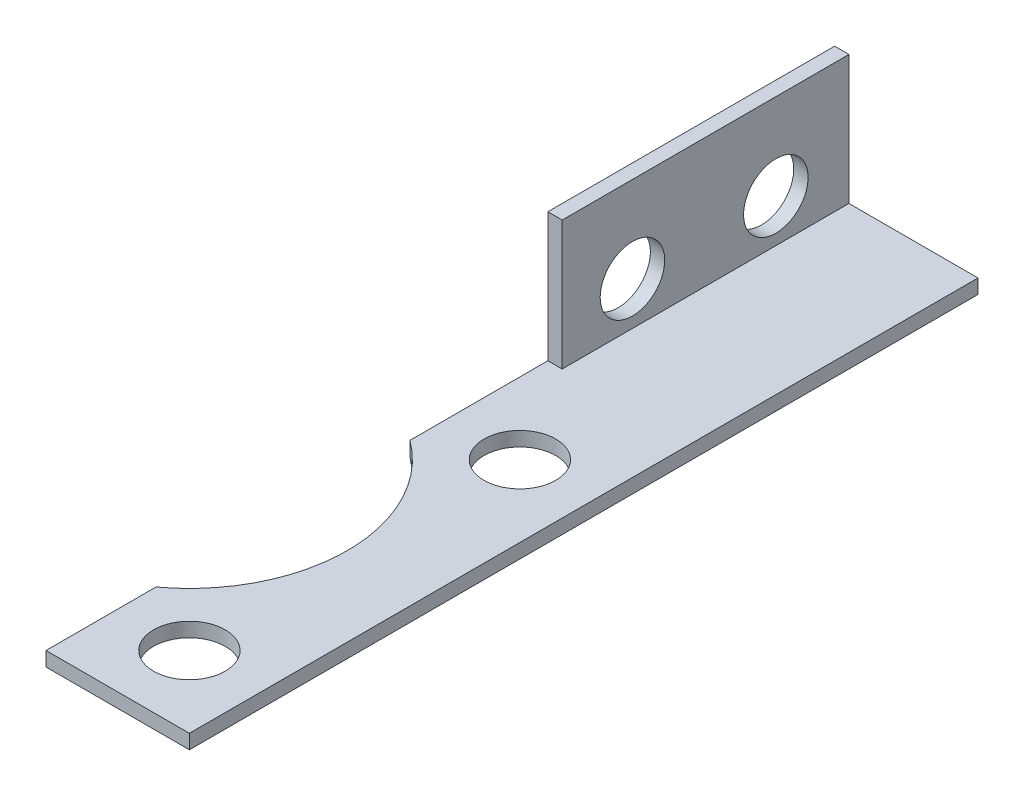
SolidWorks part; units mm, degrees
material "7075-T6 (SN)"
ref_plane "Front Plane" through (0, 0, 0) normal (0, 0, 1) x (1, 0, 0)
ref_plane "Top Plane" through (0, 0, 0) normal (0, 1, 0) x (1, 0, 0)
ref_plane "Right Plane" through (0, 0, 0) normal (1, 0, 0) x (0, 0, -1)
sketch "Sketch1" plane through (0, 0, 0) normal (0, 0, 1) x (1, 0, 0)
  line L0 (0, 10) -> (0, 0)
  line L1 (0, 0) -> (10, 0)
  line L2 (10, 0) -> (10, 1)
  line L3 (10, 1) -> (1, 1)
  line L4 (1, 1) -> (1, 10)
  line L5 (1, 10) -> (0, 10)
  dimension "D1" = 10
  dimension "D2" = 1
extrude "Boss-Extrude1" add sketch "Sketch1" along normal blind 55
sketch "Sketch2" plane through (0, 1, 0) normal (0, 1, 0) x (1, 0, 0)
  line L0 (10, -55) -> (1, -55) construction
  line L1 (10, -55) -> (10, 0) construction
  line L2 (-6.525, -26.95) -> (-6.525, -50) construction
  line L3 (-16.8017, -38.475) -> (10.6939, -38.475) construction
  line L4 (-2.7555, -28.141) -> (-2.7555, -48.809)
  circle A0 centre (5, -50) radius 2.5
  circle A1 centre (5, -26.95) radius 2.5
  arc A2 (-2.7555, -28.141) -> (-2.7555, -48.809) centre (-6.525, -38.475) cw
  dimension "D1" = 5
  dimension "D4" = 23.05
  dimension "D6" = 11
  dimension "D2" = 5
  dimension "D3" = 5
  dimension "D5" = 23.05
extrude "Cut-Extrude1" cut sketch "Sketch2" against normal through all
sketch "Sketch3" plane through (0, 0, 55) normal (0, 0, 1) x (1, 0, 0)
  line L1 (0, 10) -> (1, 10)
  line L2 (0, 10) -> (0, 1)
  line L3 (0, 1) -> (1, 1)
  line L4 (1, 10) -> (1, 1)
extrude "Cut-Extrude2" cut sketch "Sketch3" against normal blind 35
sketch "Sketch4" plane through (0, 0, 0) normal (-1, 0, 0) x (0, 0, 1)
  line L0 (0, 10) -> (0, 0) construction
  line L1 (29.6192, 0) -> (0, 0) construction
  circle A0 centre (5.1, 4) radius 2.25
  circle A1 centre (15.1, 4) radius 2.25
  dimension "D3" = 4.5
  dimension "D1" = 5.1
  dimension "D2" = 10
  dimension "D4" = 4
extrude "Cut-Extrude3" cut sketch "Sketch4" against normal through all
